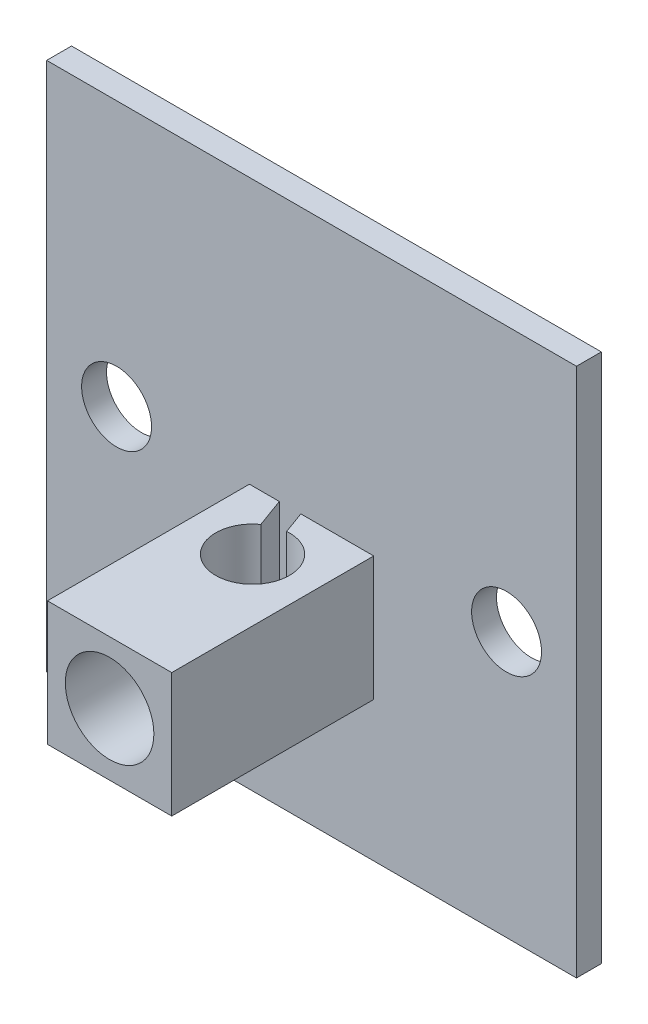
SolidWorks part; units mm, degrees
ref_plane "Front Plane" through (0, 0, 0) normal (0, 0, 1) x (1, 0, 0)
ref_plane "Top Plane" through (0, 0, 0) normal (0, 1, 0) x (1, 0, 0)
ref_plane "Right Plane" through (0, 0, 0) normal (1, 0, 0) x (0, 0, -1)
sketch "Sketch1" plane through (0, 0, 0) normal (0, 0, 1) x (1, 0, 0)
  line L0 (-16.3676, 0) -> (16.3676, 0) construction
  line L1 (-17.05, 17.05) -> (17.05, 17.05)
  line L2 (-17.05, 17.05) -> (-17.05, -17.05)
  line L3 (-17.05, -17.05) -> (17.05, -17.05)
  line L4 (17.05, 17.05) -> (17.05, -17.05)
  line L7 (0, 22.3608) -> (0, -21.2884) construction
  circle A4 centre (-12.55, 0) radius 2.25
  circle A5 centre (12.55, 0) radius 2.25
  point P6 (0, 0)
  point P8 (17.05, 0)
  point P9 (0, 17.05)
  dimension "D8" = 4.5
  dimension "D1" = 34.1
  dimension "D4" = 4.5
  dimension "D6" = 4.5
  dimension "D2" = 34.1
extrude "Boss-Extrude1" add sketch "Sketch1" along normal blind 1.6
sketch "Sketch2" plane through (0, 0, 1.6) normal (0, 0, 1) x (1, 0, 0)
  line L0 (-17.05, -17.05) -> (17.05, -17.05) construction
  line L1 (-4, -0.05) -> (4, -0.05)
  line L2 (-4, -0.05) -> (-4, -17.05)
  line L3 (-4, -17.05) -> (4, -17.05)
  line L4 (4, -0.05) -> (4, -17.05)
  line L6 (-8.1203, -8.55) -> (9.5292, -8.55) construction
  line L7 (0, 13.3499) -> (0, -12.8859) construction
  dimension "D1" = 4
  dimension "D2" = 8.5
  dimension "D3" = 8.5
  dimension "D4" = 4
extrude "Boss-Extrude2" add sketch "Sketch2" along normal blind 13
sketch "Sketch12" plane through (0, -0.05, 0) normal (0, 1, 0) x (1, 0, 0)
  line L0 (0, 1.6679) -> (0, -16.157) construction
  line L3 (17.05, -1.6) -> (-17.05, -1.6) construction
  circle A0 centre (0, -5.4) radius 2.375
  dimension "D1" = 4.75
  dimension "D2" = 3.8
extrude "Cut-Extrude3" cut sketch "Sketch12" against normal through all
sketch "Sketch13" plane through (0, -0.05, 0) normal (0, 1, 0) x (1, 0, 0)
  line L2 (-1.3921, -3.4758) -> (-2.0748, -1.6)
  line L3 (-1.3921, -3.4758) -> (-0.1705, -3.0311)
  line L4 (-0.1705, -3.0311) -> (-0.6914, -1.6)
  line L5 (-2.0748, -1.6) -> (-0.6914, -1.6)
  line L6 (1.9524, -10.7643) -> (0, -5.4) construction
  line L8 (17.05, -1.6) -> (-17.05, -1.6) construction
  line L9 (0, -5.4) -> (-1.9475, -0.0494) construction
  circle A0 centre (0, -5.4) radius 2.375 construction
  circle A1 centre (0, -5.4) radius 2.375 construction
  point P13 (-0.7813, -3.2534)
  point P20 (-1.3831, -1.6)
  dimension "D1" = 70
  dimension "D2" = 1.3
extrude "Cut-Extrude4" cut sketch "Sketch13" against normal blind 12
sketch "Sketch14" plane through (0, 0, 14.6) normal (0, 0, 1) x (1, 0, 0)
  line L0 (0, 4.4002) -> (0, -20.845) construction
  line L1 (-4, -17.05) -> (4, -17.05) construction
  line L2 (4, -0.05) -> (-4, -0.05) construction
  line L3 (-4, -0.05) -> (-4, -17.05) construction
  circle A0 centre (0, -12.55) radius 2.85
  circle A1 centre (0, -4.05) radius 2.85
  dimension "D2" = 5.7
  dimension "D3" = 4.5
  dimension "D4" = 4
  dimension "D5" = 4
extrude "Cut-Extrude9" cut sketch "Sketch14" against normal blind 5.7
sketch "Sketch15" plane through (0, 0, 8.9) normal (0, 0, 1) x (1, 0, 0)
  circle A0 centre (0, -4.05) radius 1.85
  circle A1 centre (0, -12.55) radius 1.85
  circle A2 centre (0, -4.05) radius 2.85 construction
  circle A3 centre (0, -12.55) radius 2.85 construction
  dimension "D1" = 3.7
extrude "Cut-Extrude10" cut sketch "Sketch15" against normal up to next
sketch "Sketch18" plane through (-4, 0, 0) normal (-1, 0, 0) x (0, 0, 1)
  line L0 (5.6, -17.05) -> (29.1544, 6.5044) construction
  line L1 (14.6, -17.05) -> (1.6, -17.05) construction
  line L2 (3.025, -17.05) -> (7.775, -17.05) construction
  line L3 (14.6, -17.05) -> (1.6, -17.05) construction
  line L4 (1.6, -0.05) -> (1.6, -17.05) construction
  dimension "D1" = 45
  dimension "D2" = 4
sketch "Sketch19" plane through (-4, 0, 0) normal (-1, 0, 0) x (0, 0, 1)
  line L0 (5.6, -17.05) -> (29.1544, 6.5044) construction
  line L1 (14.6, -8.05) -> (1.6, -8.05)
  line L2 (14.6, -8.05) -> (14.6, -17.05)
  line L3 (14.6, -17.05) -> (1.6, -17.05)
  line L4 (1.6, -8.05) -> (1.6, -17.05)
  line L5 (14.6, -0.05) -> (14.6, -17.05) construction
  line L6 (1.6, -0.05) -> (1.6, -17.05) construction
extrude "Cut-Extrude11" cut sketch "Sketch19" against normal through all
